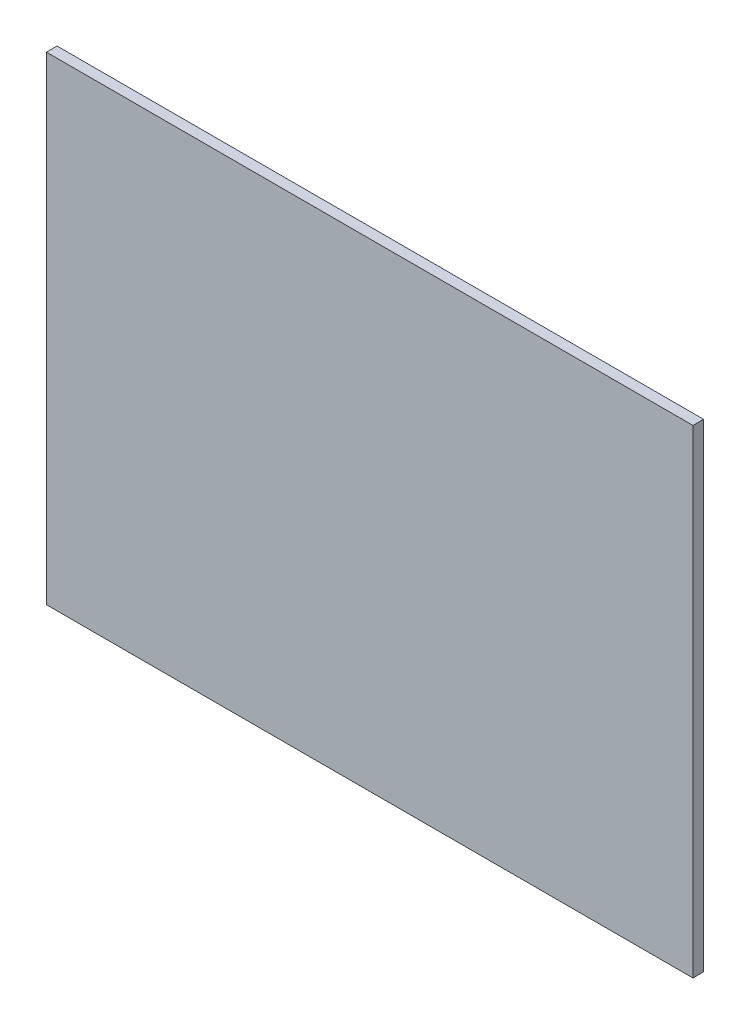
SolidWorks part; units mm, degrees
ref_plane "前视基准面" through (0, 0, 0) normal (0, 0, 1) x (1, 0, 0)
ref_plane "上视基准面" through (0, 0, 0) normal (0, 1, 0) x (1, 0, 0)
ref_plane "右视基准面" through (0, 0, 0) normal (1, 0, 0) x (0, 0, -1)
sketch "草图1" plane through (0, 0, 0) normal (0, 0, 1) x (1, 0, 0)
  line L1 (152, -112.5) -> (-152, -112.5)
  line L2 (152, -112.5) -> (152, 112.5)
  line L3 (152, 112.5) -> (-152, 112.5)
  line L4 (-152, -112.5) -> (-152, 112.5)
  line L5 (152, -112.5) -> (-152, 112.5) construction
  line L6 (152, 112.5) -> (-152, -112.5) construction
  point P0 (0, 0)
  dimension "D1" = 304
  dimension "D2" = 225
extrude "凸台-拉伸1" add sketch "草图1" along normal mid plane 5
